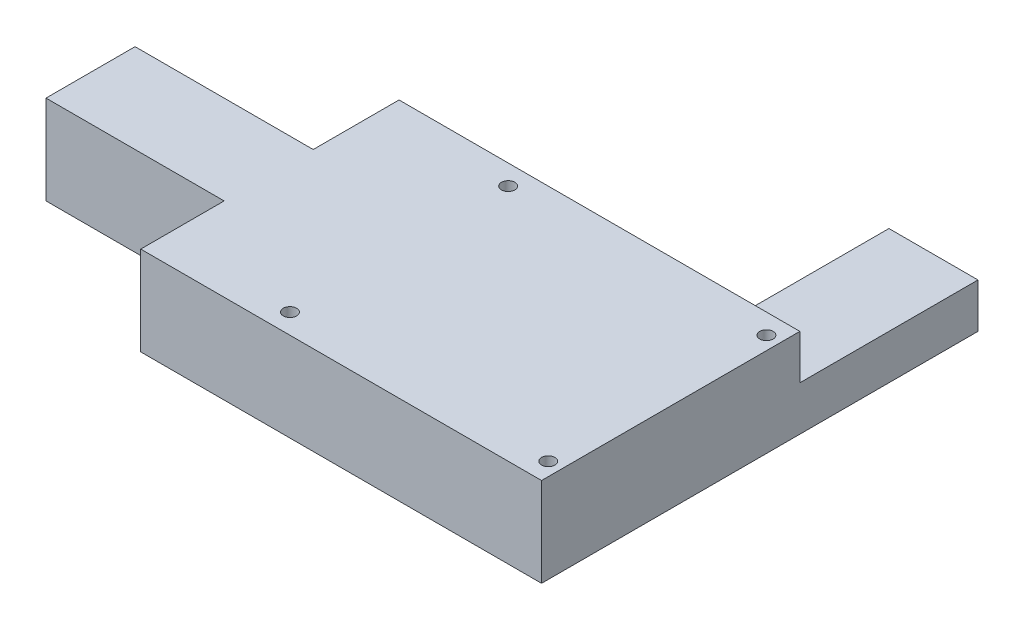
SolidWorks part; units mm, degrees
ref_plane "Front" through (0, 0, 0) normal (0, 0, 1) x (1, 0, 0)
ref_plane "Top" through (0, 0, 0) normal (0, 1, 0) x (1, 0, 0)
ref_plane "Right" through (0, 0, 0) normal (1, 0, 0) x (0, 0, -1)
sketch "Sketch1" plane through (0, 0, 0) normal (0, 1, 0) x (1, 0, 0)
  line L1 (-45, -29) -> (45, -29)
  line L2 (-45, -29) -> (-45, 29)
  line L3 (-45, 29) -> (45, 29)
  line L4 (45, -29) -> (45, 29)
  line L5 (-45, -29) -> (45, 29) construction
  line L6 (-45, 29) -> (45, -29) construction
  point P0 (0, 0)
  dimension "D1" = 58
  dimension "D2" = 90
extrude "Boss-Extrude1" add sketch "Sketch1" along normal blind 20
sketch "Sketch2" plane through (0, 20, 0) normal (0, 1, 0) x (1, 0, 0)
  line L0 (45, -29) -> (45, 29) construction
  circle A0 centre (42, 24.5) radius 1.5
  circle A1 centre (42, -24.5) radius 1.5
  circle A2 centre (-16, 24.5) radius 1.5
  circle A3 centre (-16, -24.5) radius 1.5
  dimension "D1" = 3
  dimension "D3" = 2
  dimension "D2" = 24.5
  dimension "D4" = 3
extrude "Cut-Extrude1" cut sketch "Sketch2" against normal blind 20
sketch "Sketch3" plane through (0, 0, -29) normal (0, 0, -1) x (-1, 0, 0)
  line L0 (-45, 20) -> (-45, 0) construction
  line L1 (-25, 10) -> (-45, 10)
  line L2 (-25, 10) -> (-25, 0)
  line L3 (-25, 0) -> (-45, 0)
  line L4 (-45, 10) -> (-45, 0)
  line L5 (-25, 10) -> (-45, 0) construction
  line L6 (-25, 0) -> (-45, 10) construction
  line L7 (-45, 0) -> (45, 0) construction
  point P0 (-35, 5)
  dimension "D1" = 20
  dimension "D2" = 10
  dimension "D3" = 10
  dimension "D4" = 5
extrude "Boss-Extrude2" add sketch "Sketch3" along normal blind 40
sketch "Sketch4" plane through (-45, 0, 0) normal (-1, 0, 0) x (0, 0, 1)
  line L0 (-29, 20) -> (29, 20) construction
  line L1 (10.2725, 0) -> (-9.7275, 0)
  line L2 (10.2725, 0) -> (10.2725, 20)
  line L3 (10.2725, 20) -> (-9.7275, 20)
  line L4 (-9.7275, 0) -> (-9.7275, 20)
  line L5 (10.2725, 0) -> (-9.7275, 20) construction
  line L6 (10.2725, 20) -> (-9.7275, 0) construction
  point P0 (0.2725, 10)
  dimension "D1" = 20
  dimension "D2" = 20
  dimension "D3" = 10
extrude "Boss-Extrude3" add sketch "Sketch4" along normal blind 40
